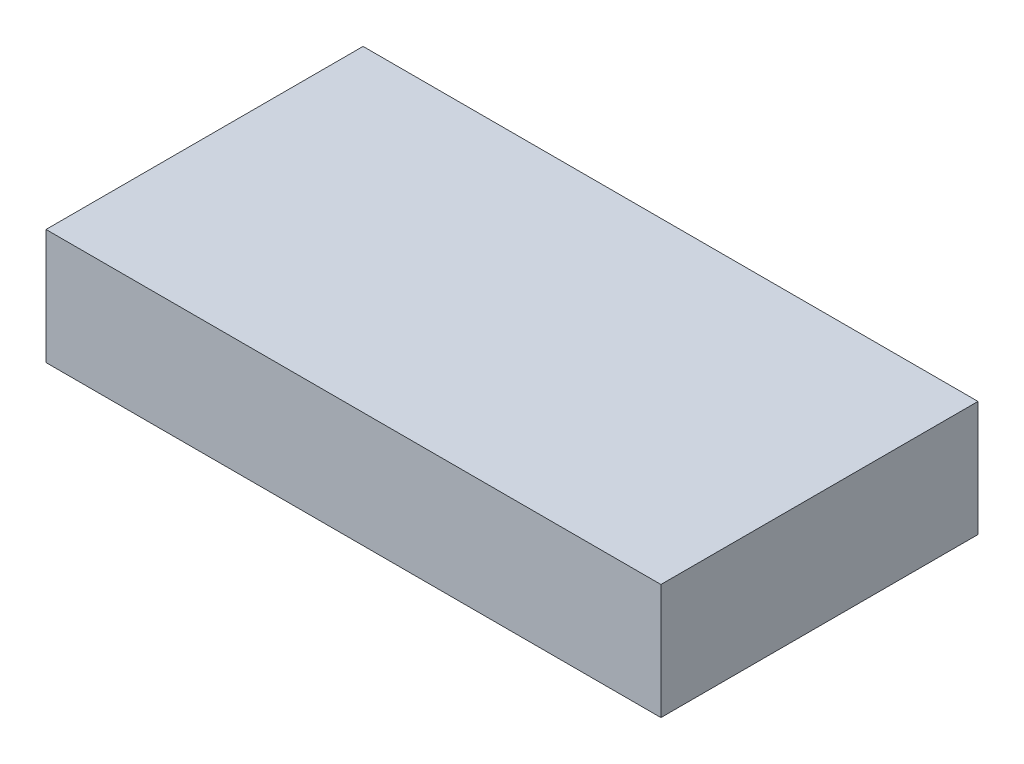
SolidWorks part; units mm, degrees
ref_plane "Front Plane" through (0, 0, 0) normal (0, 0, 1) x (1, 0, 0)
ref_plane "Top Plane" through (0, 0, 0) normal (0, 1, 0) x (1, 0, 0)
ref_plane "Right Plane" through (0, 0, 0) normal (1, 0, 0) x (0, 0, -1)
sketch "Sketch1" plane through (0, 0, 0) normal (0, 1, 0) x (1, 0, 0)
  line L1 (-24.0941, -3.1373) -> (39.9059, -3.1373)
  line L2 (-24.0941, -3.1373) -> (-24.0941, -36.1373)
  line L3 (-24.0941, -36.1373) -> (39.9059, -36.1373)
  line L4 (39.9059, -3.1373) -> (39.9059, -36.1373)
  dimension "D1" = 64
  dimension "D2" = 33
extrude "Boss-Extrude1" add sketch "Sketch1" along normal blind 12
